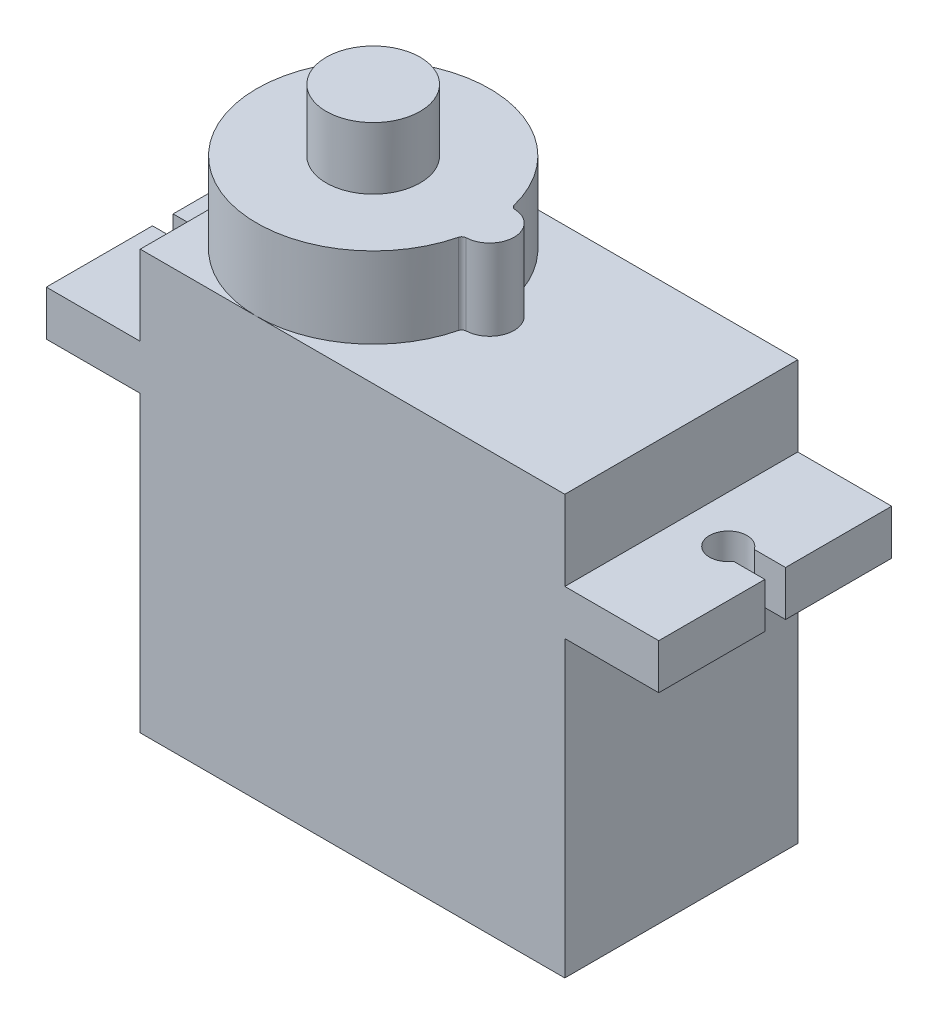
SolidWorks part; units mm, degrees
ref_plane "Front Plane" through (0, 0, 0) normal (0, 0, 1) x (1, 0, 0)
ref_plane "Top Plane" through (0, 0, 0) normal (0, 1, 0) x (1, 0, 0)
ref_plane "Right Plane" through (0, 0, 0) normal (1, 0, 0) x (0, 0, -1)
sketch "Sketch3" plane through (0, 0, 0) normal (0, 1, 0) x (1, 0, 0)
  line L1 (11.3, 6.2) -> (-11.3, 6.2)
  line L2 (11.3, 6.2) -> (11.3, -6.2)
  line L3 (11.3, -6.2) -> (-11.3, -6.2)
  line L4 (-11.3, 6.2) -> (-11.3, -6.2)
  line L5 (11.3, 6.2) -> (-11.3, -6.2) construction
  line L6 (11.3, -6.2) -> (-11.3, 6.2) construction
  point P0 (0, 0)
  dimension "D1" = 22.6
  dimension "D2" = 12.4
extrude "Boss-Extrude1" add sketch "Sketch3" along normal blind 22.3
sketch "Sketch4" plane through (0, 0, 6.2) normal (0, 0, 1) x (1, 0, 0)
  line L0 (11.3, 22.3) -> (11.3, 0) construction
  line L1 (11.3, 18.05) -> (16.3, 18.05)
  line L2 (11.3, 18.05) -> (11.3, 15.65)
  line L3 (11.3, 15.65) -> (16.3, 15.65)
  line L4 (16.3, 18.05) -> (16.3, 15.65)
  line L5 (-11.3, 22.3) -> (11.3, 22.3) construction
  line L6 (0, 0) -> (0, 13.9537) construction
  line L7 (-16.3, 18.05) -> (-16.3, 15.65)
  line L8 (-11.3, 15.65) -> (-16.3, 15.65)
  line L9 (-11.3, 18.05) -> (-11.3, 15.65)
  line L10 (-11.3, 18.05) -> (-16.3, 18.05)
  dimension "D1" = 4.25
  dimension "D2" = 2.4
  dimension "D3" = 5
extrude "Boss-Extrude2" add sketch "Sketch4" against normal up to vertex (12.4 mm away)
sketch "Sketch5" plane through (0, 18.05, 0) normal (0, 1, 0) x (1, 0, 0)
  line L0 (13.8, 0) -> (0, 0) construction
  line L1 (14.6352, 0.55) -> (16.3, 0.55)
  line L2 (16.3, 6.2) -> (16.3, -6.2) construction
  line L3 (16.3, 0.55) -> (16.3, -0.55)
  line L4 (16.3, -0.55) -> (14.6352, -0.55)
  arc A0 (14.6352, 0.55) -> (14.6352, -0.55) centre (13.8, 0) ccw
  dimension "D1" = 1.1
  dimension "D2" = 2
  dimension "D3" = 2.5
extrude "Cut-Extrude1" cut sketch "Sketch5" against normal blind 22.3
mirror "Mirror1" about plane through (0, 0, 0) normal (1, 0, 0) of "Cut-Extrude1"
sketch "Sketch7" plane through (0, 22.3, 0) normal (0, 1, 0) x (1, 0, 0)
  line L0 (-11.3, 6.2) -> (-11.3, -6.2) construction
  arc A0 (0.9186, 1.4888) -> (0.9186, -1.4888) centre (-5.1, 0) ccw
  arc A1 (1.1514, -1.299) -> (1.1514, 1.299) centre (1.1, 0) ccw
  arc A2 (1.1514, 1.299) -> (0.9186, 1.4888) centre (1.1613, 1.5488) cw
  arc A3 (1.1514, -1.299) -> (0.9186, -1.4888) centre (1.1613, -1.5488) ccw
  dimension "D1" = 12.4
  dimension "D2" = 2.6
  dimension "D3" = 0.25
extrude "Boss-Extrude3" add sketch "Sketch7" along normal blind 4.3
sketch "Sketch8" plane through (0, 26.6, 0) normal (0, 1, 0) x (1, 0, 0)
  circle A0 centre (-5.1, 0) radius 2.5
  dimension "D1" = 5
extrude "Boss-Extrude4" add sketch "Sketch8" along normal blind 3.3
sketch "Sketch9" plane through (-11.3, 0, 0) normal (-1, 0, 0) x (0, 0, 1)
  circle A0 centre (0, 4.5) radius 0.6
  circle A1 centre (1.2, 4.5) radius 0.6
  circle A2 centre (-1.2, 4.5) radius 0.6
  dimension "D1" = 1.2
  dimension "D2" = 4.5
extrude "Boss-Extrude6" add sketch "Sketch9" along normal blind 3.3 separate body contours A2 | A0 | A1
